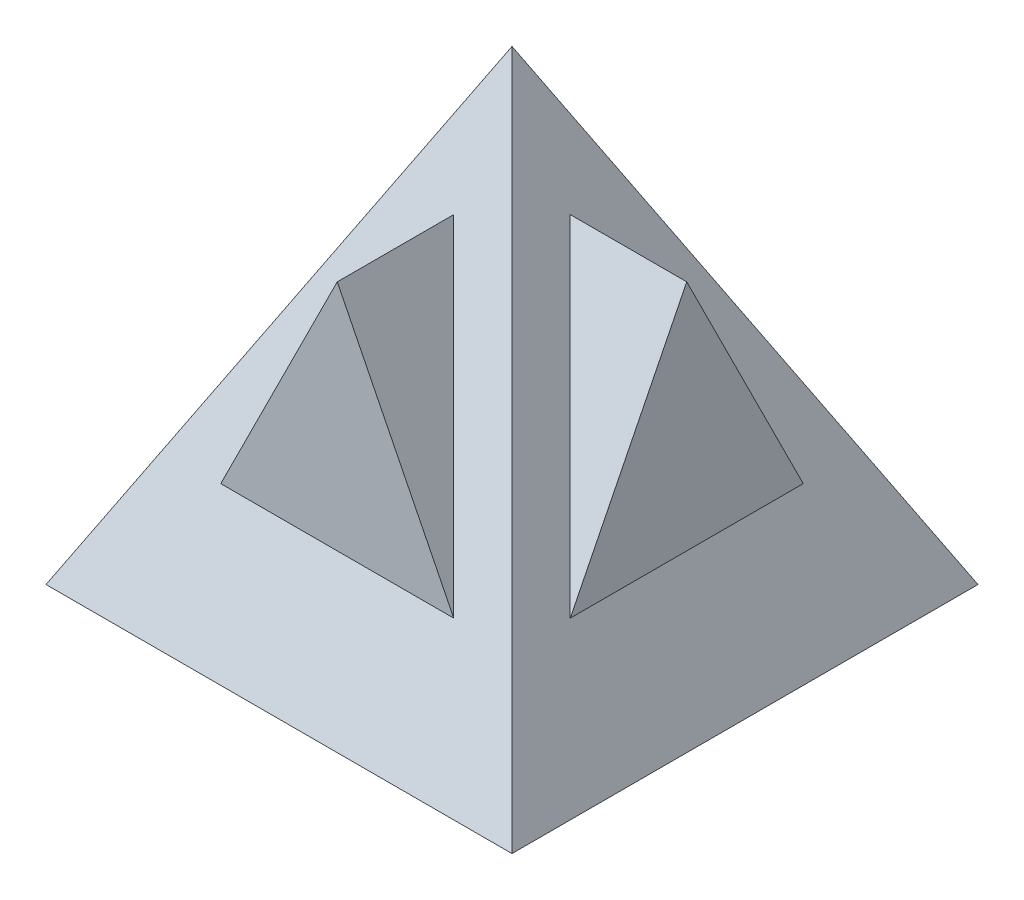
SolidWorks part; units mm, degrees
ref_plane "Front Plane" through (0, 0, 0) normal (0, 0, 1) x (1, 0, 0)
ref_plane "Top Plane" through (0, 0, 0) normal (0, 1, 0) x (1, 0, 0)
ref_plane "Right Plane" through (0, 0, 0) normal (1, 0, 0) x (0, 0, -1)
sketch "Sketch1" plane through (0, 0, 0) normal (0, 1, 0) x (1, 0, 0)
  line L1 (-4, -4) -> (4, -4)
  line L2 (-4, -4) -> (-4, 4)
  line L3 (-4, 4) -> (4, 4)
  line L4 (4, -4) -> (4, 4)
  point P4 (0, 0)
  point P5 (4, 0)
  point P6 (0, 4)
  dimension "D1" = 8
  dimension "D2" = 8
sketch "Sketch3" plane through (0, 0, 0) normal (0, 0, 1) x (1, 0, 0)
  point P0 (0, 8)
  dimension "D1" = 8
loft "Loft1" add profiles "Sketch3", "Sketch1"
sketch "Sketch5" plane through (0, 0, 0) normal (0, 0, 1) x (1, 0, 0)
  line L0 (0, 6) -> (-2, 2)
  line L1 (-2, 2) -> (2, 2)
  line L2 (2, 2) -> (0, 6)
  line L3 (0, 8) -> (4, 0) construction
  line L4 (0, 8) -> (-4, 0) construction
  dimension "D1" = 2
  dimension "D2" = 4
extrude "Boss-Extrude1" add sketch "Sketch5" along normal blind 3 separate body
move or copy body "Body-Move/Copy1" bodies to move or copy 102 copy yes number of copies 1 rotation origin (0, 0, 0) rotation axis (0, 1, 0) rotation angle 90
combine bodies "Combine1" operation type add bodies to combine 101 102 103
